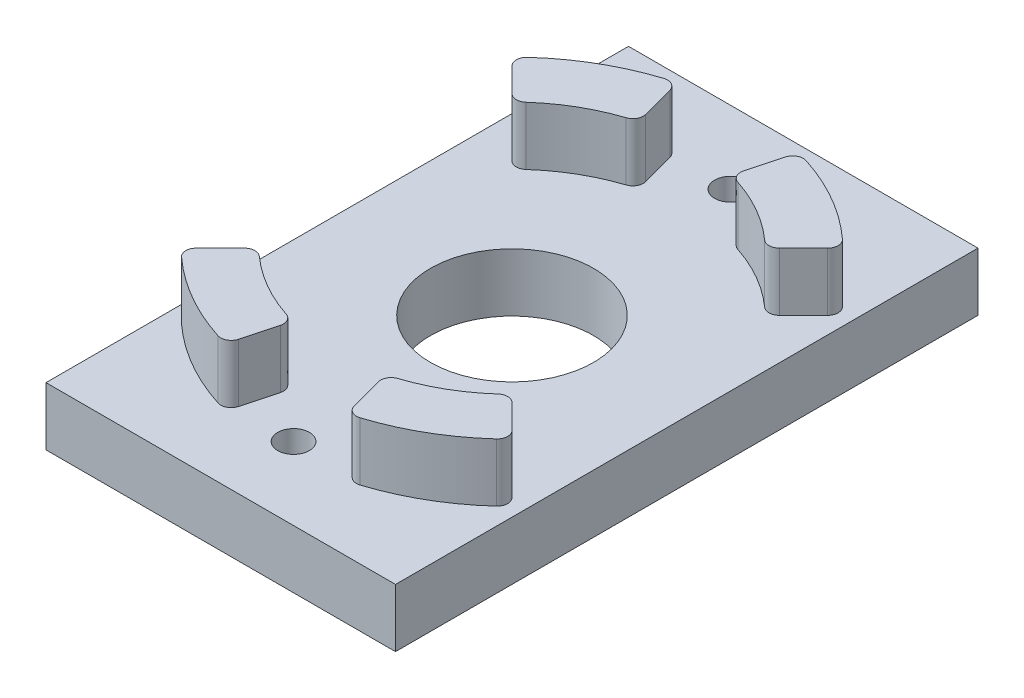
SolidWorks part; units mm, degrees
ref_plane "Front Plane" through (0, 0, 0) normal (0, 0, 1) x (1, 0, 0)
ref_plane "Top Plane" through (0, 0, 0) normal (0, 1, 0) x (1, 0, 0)
ref_plane "Right Plane" through (0, 0, 0) normal (1, 0, 0) x (0, 0, -1)
sketch "Sketch1" plane through (0, 0, 0) normal (0, 1, 0) x (1, 0, 0)
  line L1 (-19.05, -31.75) -> (19.05, -31.75)
  line L2 (-19.05, -31.75) -> (-19.05, 31.75)
  line L3 (-19.05, 31.75) -> (19.05, 31.75)
  line L4 (19.05, -31.75) -> (19.05, 31.75)
  line L5 (-19.05, -31.75) -> (19.05, 31.75) construction
  line L6 (-19.05, 31.75) -> (19.05, -31.75) construction
  point P0 (0, 0)
  dimension "D1" = 63.5
  dimension "D2" = 38.1
extrude "Boss-Extrude1" add sketch "Sketch1" along normal blind 6.35
sketch "Sketch2" plane through (0, 6.35, 0) normal (0, 1, 0) x (1, 0, 0)
  line L0 (0, 0) -> (-18.0324, 18.0324) construction
  line L1 (-18.0324, 18.0324) -> (-13.7937, 13.7937)
  line L2 (-6.6003, 24.6327) -> (0, 0) construction
  line L3 (19.05, -31.75) -> (19.05, 31.75) construction
  line L4 (-6.6003, 24.6327) -> (-5.0488, 18.8425)
  arc A0 (-5.0488, 18.8425) -> (-13.7937, 13.7937) centre (0, 0) ccw
  arc A1 (-6.6003, 24.6327) -> (-18.0324, 18.0324) centre (0, 0) ccw
  point P1 (4.6483, 25.0744)
  point P3 (-4.4474, 25.1108)
  dimension "D1" = 39.0144
  dimension "D2" = 51.0032
  dimension "D3" = 30
  dimension "D4" = 15
extrude "Boss-Extrude2" add sketch "Sketch2" along normal blind 6.35
fillet "Fillet1" radius 1.143 4 edges at (-5.0488, 9.525, -18.8425) (-6.6003, 9.525, -24.6327) (-13.7937, 9.525, -13.7937) (-18.0324, 9.525, -18.0324)
pattern_circular "CirPattern1" count 6 over 360 about axis through (0, 12.7, 0) along (0, -1, 0) skipping 1, 4 of "Boss-Extrude2", "Fillet1"
sketch "Sketch3" plane through (0, 6.35, 0) normal (0, 1, 0) x (1, 0, 0)
  circle A0 centre (0, 0) radius 8.89
  dimension "D1" = 17.78
extrude "Cut-Extrude1" cut sketch "Sketch3" against normal through all
hole_wizard "#8-32 Tapped Hole1" positions "Sketch4" profile "Sketch5" tap size "#8-32" standard "ANSI Inch" end condition up to next
sketch "Sketch4" plane through (0, 6.35, 0) normal (0, 1, 0) x (1, 0, 0)
  circle A0 centre (0, 0) radius 23.8125 construction
  point P5 (0, 23.8125)
  point P7 (0, -23.8125)
  dimension "D1" = 47.625
sketch "Sketch5" plane through (0, 6.35, 23.8125) normal (1, 0, 0) x (0, 0, 1)
  line L0 (0, 0) -> (0, 6.35)
  line L1 (0, 6.35) -> (1.7272, 6.35)
  line L2 (1.7272, 6.35) -> (1.7272, 0)
  line L5 (1.7272, 0) -> (0, 0)
  line L11 (0, -6.35) -> (0, 107.95) construction
  dimension "Thru Tap Drill Dia." = 3.4544
  dimension "Thru Tap Drill Depth" = 6.35
cosmetic thread "Hole Thread1" parameters "D2"=4.1656
cosmetic thread "Hole Thread2" parameters "D2"=4.1656
equation "\"D1@Sketch2\"=.768*2"
equation "\"D2@Sketch2\"=1.004*2"
